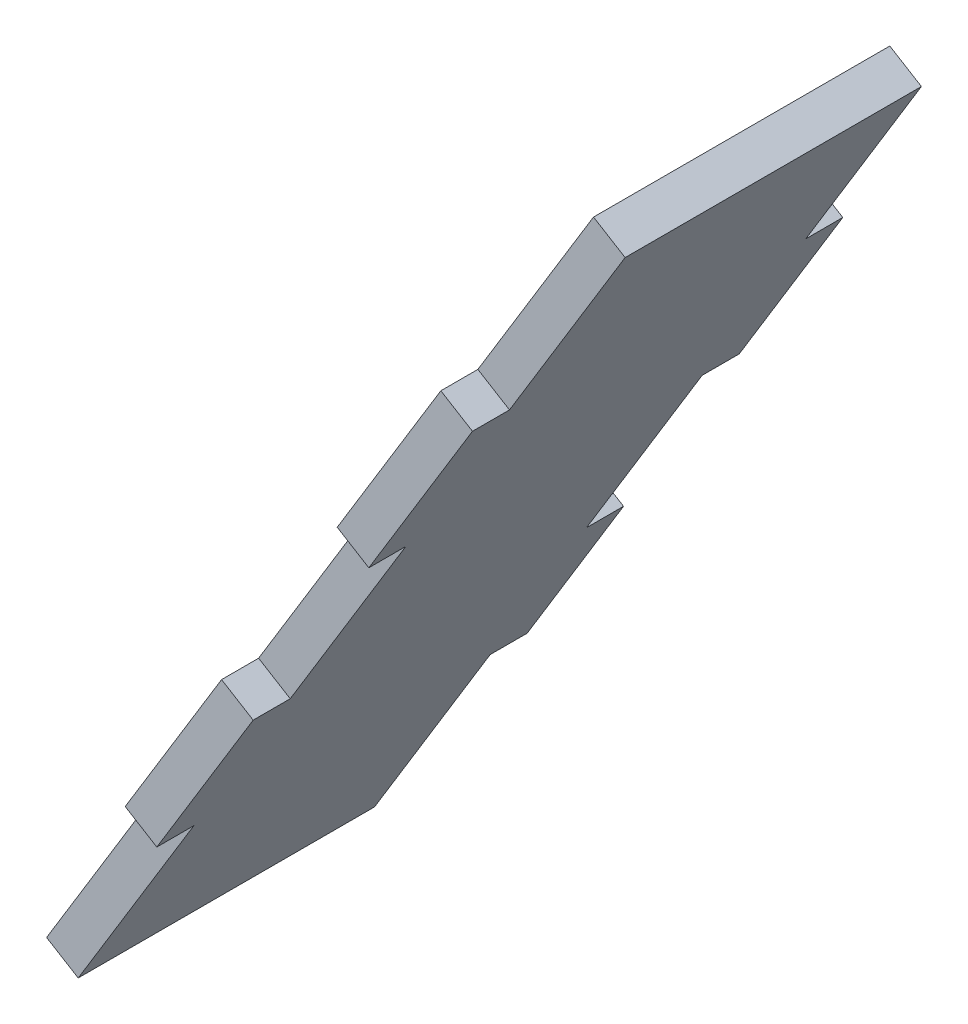
SolidWorks part; units mm, degrees
ref_plane "Front Plane" through (0, 0, 0) normal (0, 0, 1) x (1, 0, 0)
ref_plane "Top Plane" through (0, 0, 0) normal (0, 1, 0) x (1, 0, 0)
ref_plane "Right Plane" through (0, 0, 0) normal (1, 0, 0) x (0, 0, -1)
sketch "Sketch1" plane through (0, 0, 0) normal (0, 0, 1) x (1, 0, 0)
  line L0 (423.3057, 238.0672) -> (470.1939, 315)
  line L1 (470.1939, 315) -> (472.905, 313.3476)
  line L2 (472.905, 313.3476) -> (426.0169, 236.4148)
  line L3 (426.0169, 236.4148) -> (423.3057, 238.0672)
  point P2 (0, 0)
  dimension "D1" = 3.175
extrude "Boss-Extrude1" add sketch "Sketch1" against normal up to surface (31.75 mm away) contours L2 L3 L0 L1
sketch "Sketch3" plane through (205.5699, -125.2885, 0) normal (0.8539, -0.5204, 0) x (0, 0, -1)
  line L0 (3.175, 483.4075) -> (3.175, 508.7099) construction
  line L1 (0, 513.6825) -> (3.175, 513.6825)
  line L2 (0, 513.6825) -> (0, 494.6325)
  line L3 (0, 494.6325) -> (3.175, 494.6325)
  line L4 (3.175, 513.6825) -> (3.175, 494.6325)
  line L5 (28.575, 508.7099) -> (28.575, 483.4075) construction
  line L6 (31.75, 513.6825) -> (28.575, 513.6825)
  line L7 (31.75, 513.6825) -> (31.75, 494.6325)
  line L8 (31.75, 494.6325) -> (28.575, 494.6325)
  line L9 (28.575, 513.6825) -> (28.575, 494.6325)
  line L10 (3.175, 440.1438) -> (3.175, 336.6997) construction
  line L11 (0, 423.5872) -> (3.175, 423.5872)
  line L12 (0, 423.5872) -> (0, 442.6372)
  line L13 (0, 442.6372) -> (3.175, 442.6372)
  line L14 (3.175, 423.5872) -> (3.175, 442.6372)
  line L15 (28.575, 336.6997) -> (28.575, 440.1438) construction
  line L16 (28.575, 442.6372) -> (31.75, 442.6372)
  line L17 (28.575, 442.6372) -> (28.575, 423.5872)
  line L18 (28.575, 423.5872) -> (31.75, 423.5872)
  line L19 (31.75, 442.6372) -> (31.75, 423.5872)
  line L20 (28.575, 536.22) -> (28.575, 394.7255) construction
  line L21 (28.575, 477.5622) -> (31.75, 477.5622)
  line L22 (28.575, 477.5622) -> (28.575, 458.5122)
  line L23 (28.575, 458.5122) -> (31.75, 458.5122)
  line L24 (31.75, 477.5622) -> (31.75, 458.5122)
  line L25 (31.75, 513.6825) -> (31.75, 423.5872) construction
  line L26 (0, 513.6825) -> (0, 423.5872) construction
  line L27 (3.175, 458.5122) -> (0, 458.5122)
  line L28 (3.175, 458.5122) -> (3.175, 477.5622)
  line L29 (3.175, 477.5622) -> (0, 477.5622)
  line L30 (0, 458.5122) -> (0, 477.5622)
  dimension "D1" = 19.05
  dimension "D2" = 19.05
  dimension "D3" = 19.05
  dimension "D4" = 19.05
  dimension "D5" = 19.05
  dimension "D6" = 19.05
  dimension "D7" = 15.875
  dimension "D8" = 15.875
  dimension "D9" = 3.175
extrude "Cut-Extrude1" cut sketch "Sketch3" against normal blind 3.175
